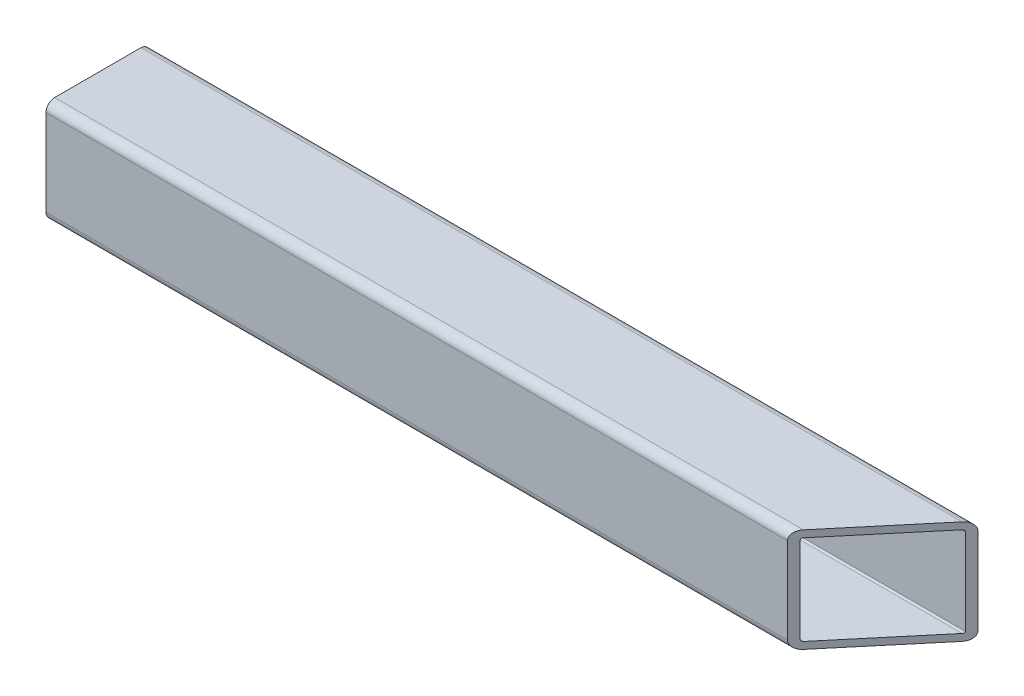
SolidWorks part; units mm, degrees
ref_plane "Front Plane" through (0, 0, 0) normal (0, 0, 1) x (1, 0, 0)
ref_plane "Top Plane" through (0, 0, 0) normal (0, 1, 0) x (1, 0, 0)
ref_plane "Right Plane" through (0, 0, 0) normal (1, 0, 0) x (0, 0, -1)
sketch "Sketch1" plane through (0, 0, 0) normal (1, 0, 0) x (0, 0, -1)
  line L1 (-15.875, 19.05) -> (15.875, 19.05)
  line L2 (-19.05, 15.875) -> (-19.05, -15.875)
  line L3 (-15.875, -19.05) -> (15.875, -19.05)
  line L4 (19.05, 15.875) -> (19.05, -15.875)
  line L5 (-19.05, 19.05) -> (19.05, -19.05) construction
  line L6 (-19.05, -19.05) -> (19.05, 19.05) construction
  arc A0 (-19.05, -15.875) -> (-15.875, -19.05) centre (-15.875, -15.875) ccw
  arc A1 (15.875, -19.05) -> (19.05, -15.875) centre (15.875, -15.875) ccw
  arc A2 (19.05, 15.875) -> (15.875, 19.05) centre (15.875, 15.875) ccw
  arc A3 (-15.875, 19.05) -> (-19.05, 15.875) centre (-15.875, 15.875) ccw
  point P0 (0, 0)
  dimension "D3" = 3.175
  dimension "D1" = 38.1
  dimension "D2" = 38.1
extrude "Extrude-Thin1" add sketch "Sketch1" along normal mid plane 304.8 thin
sketch "Sketch3" plane through (0, 19.05, 0) normal (0, 1, 0) x (1, 0, 0)
  line L0 (152.4, 15.875) -> (152.4, -15.875) construction
  line L1 (152.4, 19.05) -> (120.4303, -19.05)
  line L2 (152.4, -19.05) -> (-152.4, -19.05) construction
  dimension "D1" = 40
sketch "Sketch4" plane through (-152.4, 0, 0) normal (-1, 0, 0) x (0, 0, 1)
  line L0 (16.51, 0) -> (-16.51, 0) construction
  line L1 (16.51, 15.875) -> (16.51, -15.875) construction
  line L2 (-16.51, -15.875) -> (-16.51, 15.875) construction
  line L3 (0, 16.51) -> (0, -16.51) construction
  line L4 (-15.875, 16.51) -> (15.875, 16.51) construction
  line L5 (15.875, -16.51) -> (-15.875, -16.51) construction
extrude "Cut-Extrude1" cut sketch "Sketch3" against normal through all and the other way through all
